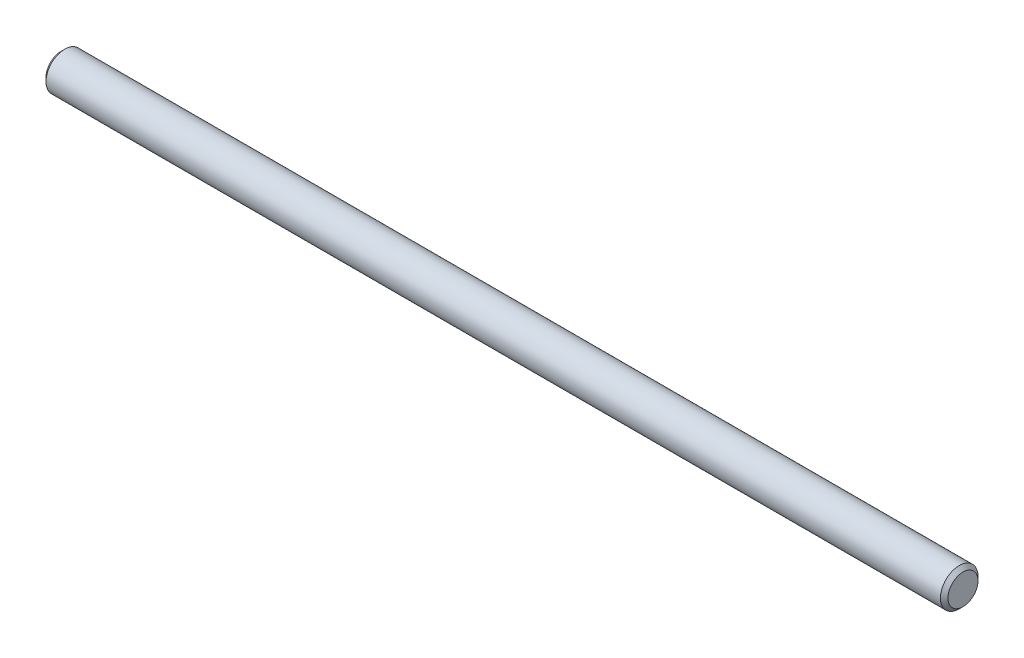
SolidWorks part; units mm, degrees
ref_plane "Front" through (0, 0, 0) normal (0, 0, 1) x (1, 0, 0)
ref_plane "Top" through (0, 0, 0) normal (0, 1, 0) x (1, 0, 0)
ref_plane "Right" through (0, 0, 0) normal (1, 0, 0) x (0, 0, -1)
sketch "Sketch1" plane through (0, 0, 0) normal (0, 0, 1) x (1, 0, 0)
  line L0 (-19.05, 0) -> (19.05, 0) construction
  line L1 (19.05, 0.7937) -> (19.05, -0.7937) construction
  line L2 (-19.05, 0.7937) -> (-19.05, -0.7937) construction
  dimension "Length" = 38.1
  dimension "Diameter" = 1.5875
sketch "Sketch2" plane through (0, 0, 0) normal (1, 0, 0) x (0, 0, -1)
  circle A0 centre (0, 0) radius 0.7937
extrude "Extrude1" add sketch "Sketch2" against normal up to vertex (19.05 mm away) and the other way up to vertex (19.05 mm away) up to point (-19.05, 0.7937, 0) other way up to point (19.05, 0.7937, 0)
chamfer "Chamfer1" distance 0.1588 angle 45 2 edges at (19.05, 0, -0.7937) (-19.05, 0, -0.7937)
equation "\"D1@Chamfer1\" = \"Diameter@Sketch1\"*.1"
